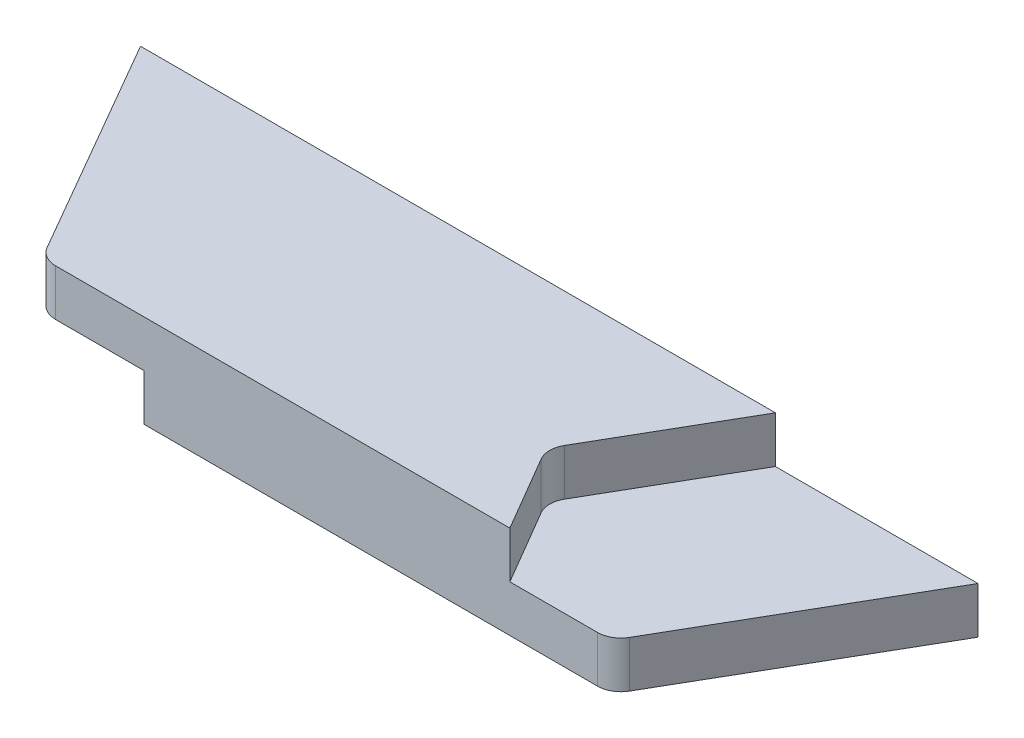
SolidWorks part; units mm, degrees
ref_plane "Спереди" through (0, 0, 0) normal (0, 0, 1) x (1, 0, 0)
ref_plane "Сверху" through (0, 0, 0) normal (0, 1, 0) x (1, 0, 0)
ref_plane "Справа" through (0, 0, 0) normal (1, 0, 0) x (0, 0, -1)
sketch "Эскиз1" plane through (0, 0, 0) normal (1, 0, 0) x (0, 0, -1)
  line L1 (0, 0) -> (50, 0)
  line L2 (0, 0) -> (0, 20)
  line L3 (0, 20) -> (50, 20)
  line L4 (50, 0) -> (50, 20)
extrude "Бобышка-Вытянуть1" add sketch "Эскиз1" along normal blind 180
sketch "Эскиз2" plane through (0, 0, 0) normal (0, -1, 0) x (1, 0, 0)
  line L1 (180, 0) -> (0, 0) construction
  line L2 (180, -50) -> (0, -50) construction
  line L3 (43.5175, -50) -> (0, -50)
  line L4 (0, -50) -> (0, 0)
  line L5 (0, 0) -> (50.699, 0)
  line L6 (60.0856, -21.3033) -> (43.5175, -50)
  line L8 (50.699, 0) -> (60.0886, -16.3085)
  arc A0 (60.0856, -21.3033) -> (60.0886, -16.3085) centre (55.7554, -18.8033) ccw
  dimension "D1" = 5
extrude "Вырез-Вытянуть1" cut sketch "Эскиз2" against normal blind 10
sketch "Эскиз3" plane through (0, 20, 0) normal (0, 1, 0) x (1, 0, 0)
  line L1 (180, 0) -> (0, 0) construction
  line L2 (119.8701, 21.2606) -> (136.4628, 50)
  line L3 (180, 50) -> (0, 50) construction
  line L4 (136.4628, 50) -> (180, 50)
  line L5 (180, 50) -> (180, 0)
  line L6 (180, 0) -> (129.3842, 0)
  line L8 (119.8846, 16.2355) -> (129.3842, 0)
  arc A0 (119.8846, 16.2355) -> (119.8701, 21.2606) centre (124.2002, 18.7606) cw
  dimension "D1" = 5
extrude "Вырез-Вытянуть2" cut sketch "Эскиз3" against normal blind 10
sketch "Эскиз4" plane through (0, 20, 0) normal (0, 1, 0) x (1, 0, 0)
  line L0 (180, 50) -> (152.5759, 2.5)
  line L1 (129.3842, 0) -> (180, 0) construction
  line L2 (148.2457, 0) -> (31.7543, 0)
  line L3 (129.3842, 0) -> (0, 0) construction
  line L4 (27.4241, 2.5) -> (0, 50)
  line L5 (0, 50) -> (0, 0) construction
  line L6 (136.4628, 50) -> (0, 50) construction
  line L7 (0, 50) -> (180, 50)
  arc A0 (152.5759, 2.5) -> (148.2457, 0) centre (148.2457, 5) cw
  arc A1 (31.7543, 0) -> (27.4241, 2.5) centre (31.7543, 5) cw
  point P15 (151.1325, 0)
  point P18 (28.8675, 0)
  dimension "D1" = 5
extrude "Вырез-Вытянуть4" cut sketch "Эскиз4" against normal through all flip side to cut
